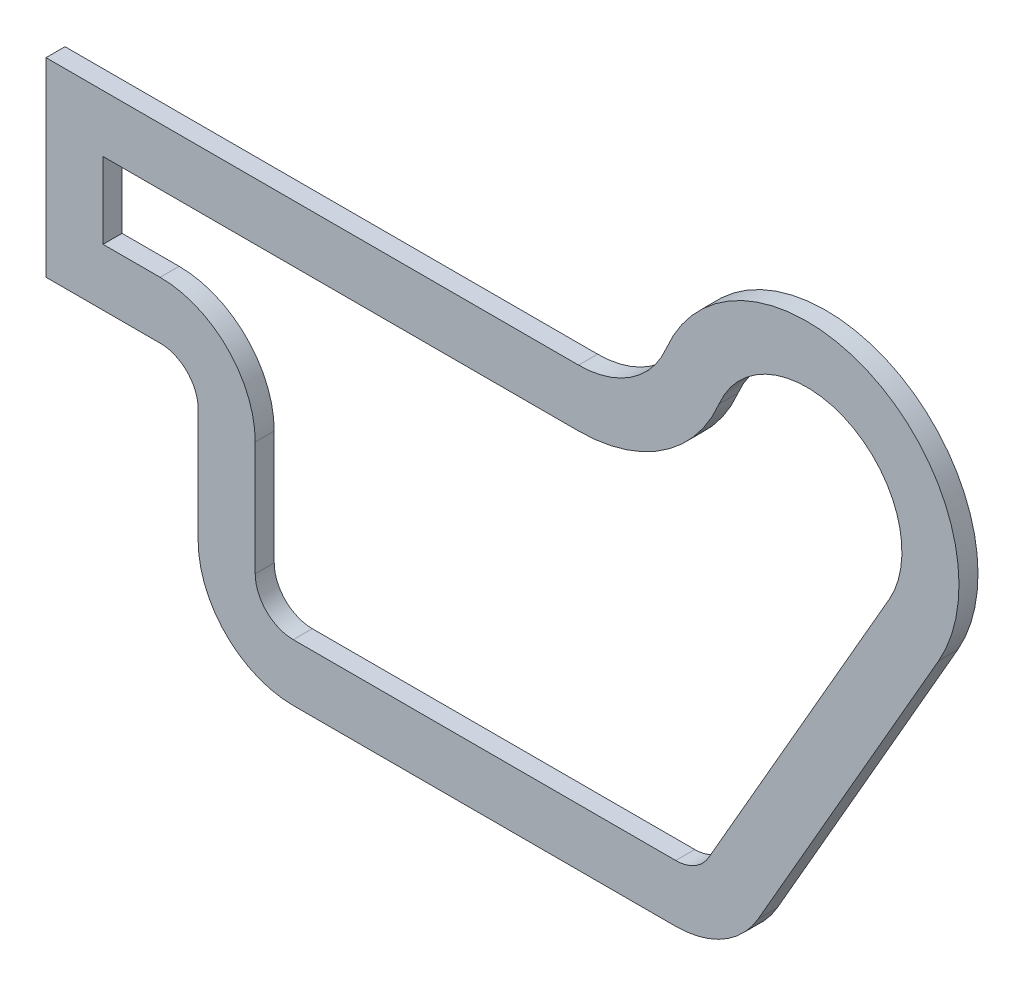
SolidWorks part; units mm, degrees
ref_plane "Front Plane" through (0, 0, 0) normal (0, 0, 1) x (1, 0, 0)
ref_plane "Top Plane" through (0, 0, 0) normal (0, 1, 0) x (1, 0, 0)
ref_plane "Right Plane" through (0, 0, 0) normal (1, 0, 0) x (0, 0, -1)
sketch "Sketch3" plane through (0, 0, 0) normal (0, 0, 1) x (1, 0, 0)
  line L0 (140, 115) -> (0, 115)
  line L1 (0, 115) -> (0, 65)
  line L2 (0, 65) -> (30, 65)
  line L3 (40, 55) -> (40, 25)
  line L4 (65, 0) -> (165.5389, 0)
  line L5 (187.21, 12.5355) -> (234.6737, 95.0567)
  arc A0 (234.6737, 95.0567) -> (163.0769, 130.3846) centre (200, 115) ccw
  arc A1 (40, 55) -> (30, 65) centre (30, 55) ccw
  arc A2 (65, 0) -> (40, 25) centre (65, 25) cw
  arc A3 (187.21, 12.5355) -> (165.5389, 0) centre (165.5389, 25) cw
  arc A4 (163.0769, 130.3846) -> (140, 115) centre (140, 140) cw
  point P14 (180, 0)
  point P17 (160, 115)
  dimension "D1" = 80
  dimension "D7" = 10
  dimension "D8" = 25
  dimension "D9" = 25
  dimension "D10" = 25
  dimension "D2" = 50
  dimension "D3" = 40
  dimension "D4" = 180
  dimension "D5" = 200
  dimension "D6" = 115
extrude "Boss-Extrude1" add sketch "Sketch3" along normal blind 5 contours L0 L1 L2 A1 L3 A2 L4 A3 L5 A0 A4
shell "Shell1" thickness 15
